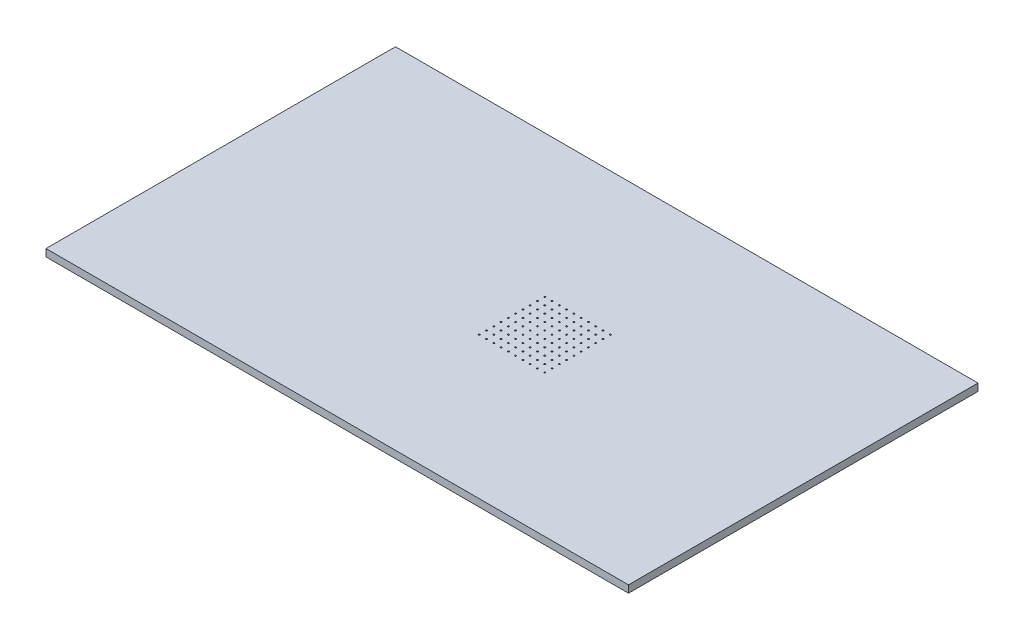
SolidWorks part; units mm, degrees
ref_plane "Front" through (0, 0, 0) normal (0, 0, 1) x (1, 0, 0)
ref_plane "Top" through (0, 0, 0) normal (0, 1, 0) x (1, 0, 0)
ref_plane "Right" through (0, 0, 0) normal (1, 0, 0) x (0, 0, -1)
sketch "Sketch2" plane through (0, 0, 0) normal (0, 1, 0) x (1, 0, 0)
  line L1 (-2851.7273, 1535.5455) -> (-819.7273, 1535.5455)
  line L2 (-2851.7273, 1535.5455) -> (-2851.7273, 316.3455)
  line L3 (-2851.7273, 316.3455) -> (-819.7273, 316.3455)
  line L4 (-819.7273, 1535.5455) -> (-819.7273, 316.3455)
  dimension "D1" = 2032
  dimension "D2" = 1219.2
extrude "Boss-Extrude1" add sketch "Sketch2" along normal blind 25.4
sketch "Sketch3" plane through (0, 25.4, 0) normal (0, 1, 0) x (1, 0, 0)
  line L0 (-1835.7273, 1535.5455) -> (-1835.7273, 811.6455) construction
  line L1 (-819.7273, 1535.5455) -> (-2851.7273, 1535.5455) construction
  line L2 (-1835.7273, 811.6455) -> (-1069.8523, 811.6455) construction
  line L3 (-819.7273, 316.3455) -> (-819.7273, 1535.5455) construction
  line L4 (-2851.7273, 316.3455) -> (-819.7273, 316.3455) construction
  dimension "D1" = 1016
  dimension "D2" = 495.3
hole_wizard "1/4-20 Tapped Hole1" positions "Sketch5" profile "Sketch4" tap size "1/4-20" standard "ANSI Inch" end condition through all
sketch "Sketch5" plane through (0, 25.4, 0) normal (0, 1, 0) x (1, 0, 0)
  point P0 (-1835.7273, 811.6455)
sketch "Sketch4" plane through (-1835.7273, 25.4, -811.6455) normal (1, 0, 0) x (0, 0, 1)
  line L0 (0, 0) -> (0, 25.4)
  line L1 (0, 25.4) -> (2.5527, 25.4)
  line L2 (2.5527, 25.4) -> (2.5527, 0)
  line L5 (2.5527, 0) -> (0, 0)
  line L11 (0, -6.35) -> (0, 107.95) construction
  dimension "Thru Tap Drill Dia." = 5.1054
  dimension "Thru Tap Drill Depth" = 25.4
cosmetic thread "Hole Thread1" parameters "D2"=6.35
pattern_linear "LPattern1" count 10 spacing 25.4 along (0, 0, -1) count 10 spacing 25.4 along (1, 0, 0) of "1/4-20 Tapped Hole1"
